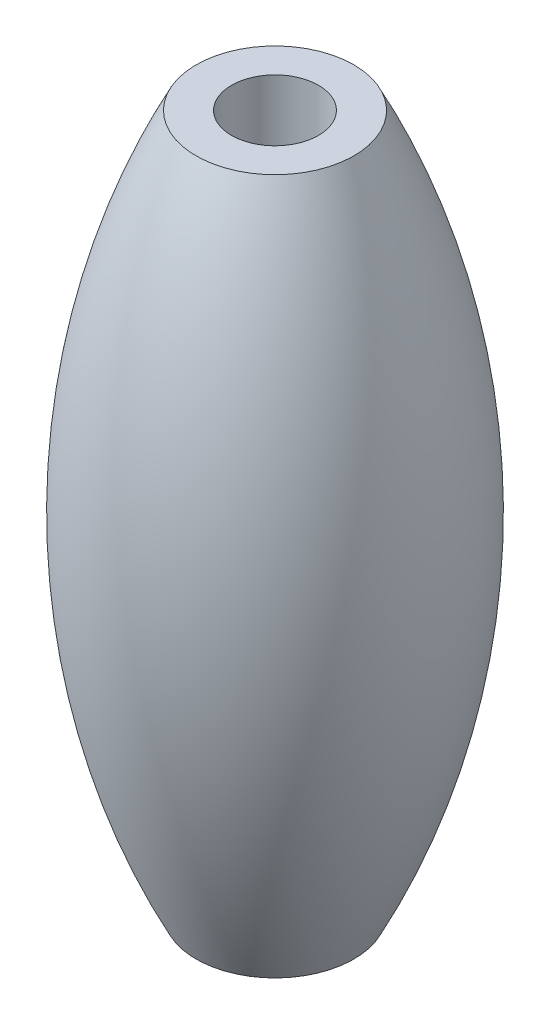
SolidWorks part; units mm, degrees
ref_plane "Front Plane" through (0, 0, 0) normal (0, 0, 1) x (1, 0, 0)
ref_plane "Top Plane" through (0, 0, 0) normal (0, 1, 0) x (1, 0, 0)
ref_plane "Right Plane" through (0, 0, 0) normal (1, 0, 0) x (0, 0, -1)
sketch "Sketch1" plane through (0, 0, 0) normal (0, 0, 1) x (1, 0, 0)
  line L0 (0, 0) -> (16.0421, 0) construction
  line L1 (0, -14) -> (0, 14)
  line L2 (0, 14) -> (3.175, 14)
  line L3 (0, -14) -> (3.175, -14)
  arc A0 (3.175, 14) -> (3.175, -14) centre (-24.6362, 0) cw
  point P8 (6.5, 0)
  dimension "D1" = 3.175
  dimension "D2" = 14
  dimension "D3" = 6.5
revolve "Revolve1" add sketch "Sketch1" angle 360 about L1
hole_wizard "Ø3.0mm Dowel Hole1" positions "Sketch4" profile "Sketch5" hole size "Ø3.0" standard "ANSI Metric" end condition through all
sketch "Sketch4" plane through (0, 14, 0) normal (0, 1, 0) x (1, 0, 0)
  point P0 (0, 0)
sketch "Sketch5" plane through (0, 14, 0) normal (1, 0, 0) x (0, 0, 1)
  line L0 (0, 0) -> (0, 28)
  line L1 (0, 28) -> (1.75, 28)
  line L2 (1.75, 28) -> (1.75, 0)
  line L5 (1.75, 0) -> (0, 0)
  line L11 (0, -6.35) -> (0, 107.95) construction
  dimension "Thru Hole Dia." = 3.5
  dimension "Thru Hole Depth" = 28
